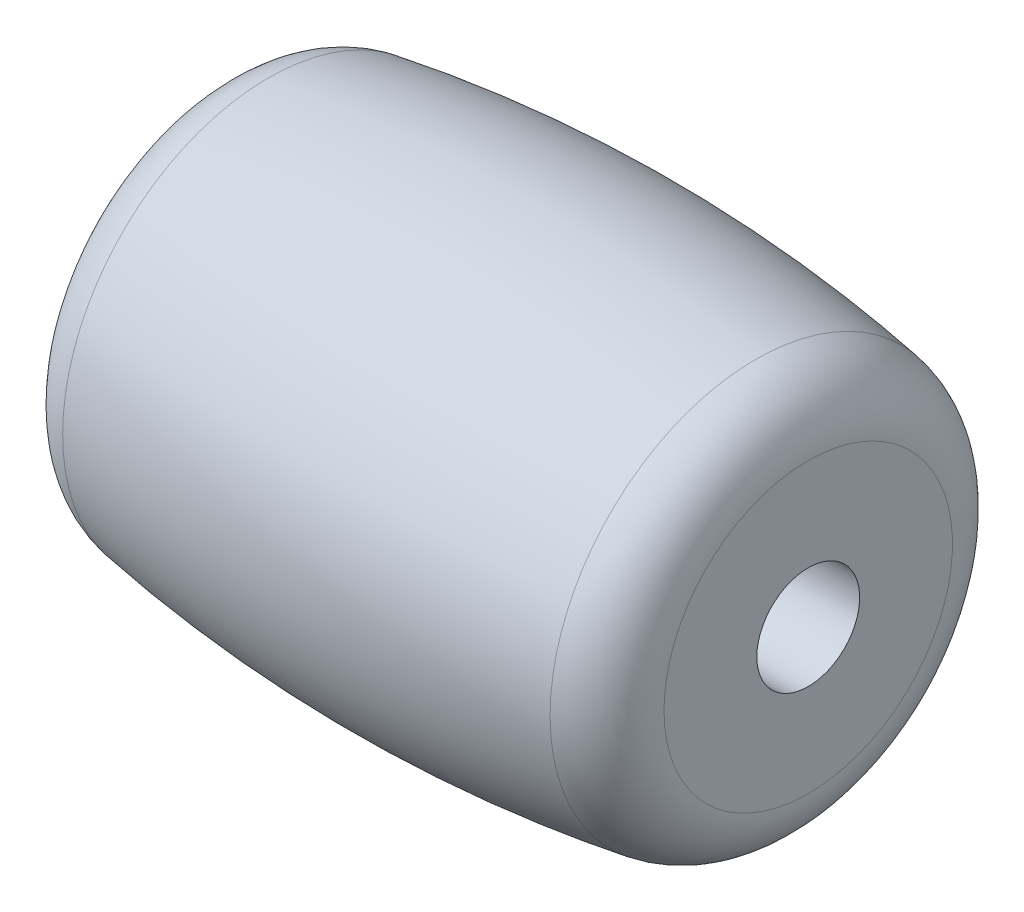
SolidWorks part; units mm, degrees
material "NEOPRENE"
ref_plane "Front Plane" through (0, 0, 0) normal (0, 0, 1) x (1, 0, 0)
ref_plane "Top Plane" through (0, 0, 0) normal (0, 1, 0) x (1, 0, 0)
ref_plane "Right Plane" through (0, 0, 0) normal (1, 0, 0) x (0, 0, -1)
ref_plane "Plane1" through (0, 0, 0) normal (0, 0, -1) x (-1, 0, 0)
sketch "Sketch1" plane through (0, 0, 0) normal (0, 0, -1) x (-1, 0, 0)
  line L0 (-9.5, 4.6276) -> (-9.5, 1.65)
  line L1 (-9.5, 1.65) -> (9.5, 1.65)
  line L2 (9.5, 1.65) -> (9.5, 4.6276)
  line L3 (-9.5031, 0) -> (9.5034, 0) construction
  arc A0 (9.5, 4.6276) -> (7.8192, 6.6019) centre (7.5, 4.6276) ccw
  arc A1 (7.8192, 6.6019) -> (-7.8192, 6.6019) centre (0, -41.7565) ccw
  arc A2 (-7.8192, 6.6019) -> (-9.5, 4.6276) centre (-7.5, 4.6276) ccw
  dimension "D1" = 2
revolve "Revolve1" add sketch "Sketch1" angle 360 about L3
